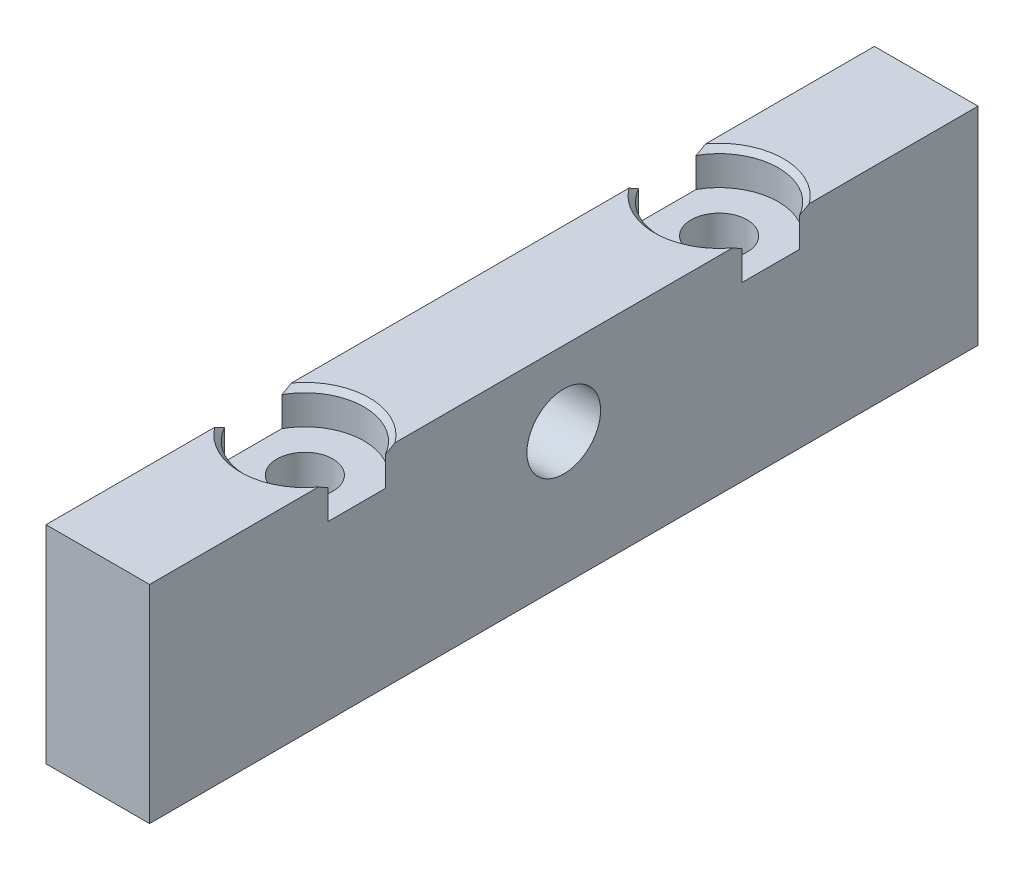
SolidWorks part; units mm, degrees
ref_plane "Front Plane" through (0, 0, 0) normal (0, 0, 1) x (1, 0, 0)
ref_plane "Top Plane" through (0, 0, 0) normal (0, 1, 0) x (1, 0, 0)
ref_plane "Right Plane" through (0, 0, 0) normal (1, 0, 0) x (0, 0, -1)
sketch "Sketch1" plane through (0, 0, 0) normal (0, 1, 0) x (1, 0, 0)
  line L1 (-4.825, 17.9112) -> (7.675, 17.9112)
  line L2 (-4.825, 17.9112) -> (-4.825, -82.0888)
  line L3 (-4.825, -82.0888) -> (7.675, -82.0888)
  line L4 (7.675, 17.9112) -> (7.675, -82.0888)
  dimension "D1" = 12.5
  dimension "D2" = 100
extrude "Boss-Extrude1" add sketch "Sketch1" along normal blind 25
sketch "Sketch2" plane through (0, 25, 0) normal (0, 1, 0) x (1, 0, 0)
  line L0 (1.425, 17.9112) -> (1.425, -82.0888) construction
  line L1 (7.675, 17.9112) -> (-4.825, 17.9112) construction
  line L2 (-4.825, -82.0888) -> (7.675, -82.0888) construction
  point P6 (1.425, -7.0888)
  point P7 (1.425, -57.0888)
  dimension "D1" = 25
  dimension "D2" = 25
hole_wizard "CBORE for 1/4 Binding Head Machine Screw1" positions "3DSketch1" profile "Sketch3" counterbore size "1/4" standard "ANSI Inch" end condition up to next
sketch3d "3DSketch1"
  point P0 (1.425, 25, 7.0888)
  point P3 (1.425, 25, 57.0888)
sketch "Sketch3" plane through (1.425, 25, 7.0888) normal (1, 0, 0) x (0, 0, 1)
  line L0 (0, 0) -> (0, 25)
  line L1 (0, 25) -> (3.3782, 25)
  line L3 (3.3782, 25) -> (3.3782, 4.191)
  line L4 (7.1437, 4.191) -> (3.3782, 4.191)
  line L5 (7.1437, 4.191) -> (7.1437, 0.635)
  line L6 (7.1437, 0.635) -> (7.7788, 0)
  line L7 (7.7788, 0) -> (0, 0)
  line L8 (-7.1437, 0.635) -> (-7.7788, 0) construction
  line L11 (0, -6.35) -> (0, 107.95) construction
  dimension "Thru Hole Dia." = 6.7564
  dimension "Thru Hole Depth" = 25
  dimension "C'Bore Dia." = 14.2875
  dimension "C'Bore Depth" = 4.191
  dimension "Near C'Sink Dia." = 15.5575
  dimension "Near C'Sink Angle" = 90
sketch "Sketch4" plane through (-4.825, 0, 0) normal (-1, 0, 0) x (0, 0, 1)
  line L0 (32.0888, 25) -> (32.0888, 0) construction
  line L1 (11.7199, 25) -> (52.4578, 25) construction
  line L2 (-17.9112, 0) -> (82.0888, 0) construction
  line L3 (-17.9112, 25) -> (82.0888, 25) construction
  circle A0 centre (32.0888, 16) radius 4.445
  dimension "D1" = 8.89
  dimension "D2" = 9
extrude "Cut-Extrude1" cut sketch "Sketch4" against normal up to next
